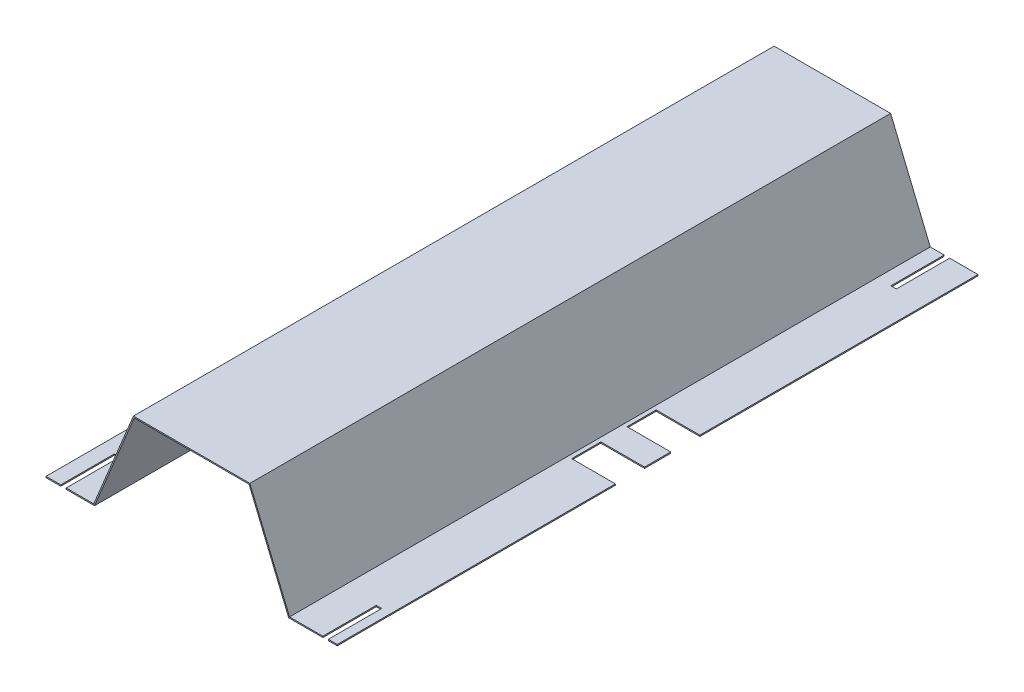
SolidWorks part; units mm, degrees
material "6061-T6 (SS)"
ref_plane "Front" through (0, 0, 0) normal (0, 0, 1) x (1, 0, 0)
ref_plane "Top" through (0, 0, 0) normal (0, 1, 0) x (1, 0, 0)
ref_plane "Right" through (0, 0, 0) normal (1, 0, 0) x (0, 0, -1)
sketch "Sketch1" plane through (0, 0, 0) normal (0, 0, 1) x (1, 0, 0)
  line L0 (-0.2237, 63.6222) -> (51.6461, 189.022)
  line L1 (51.6461, 189.022) -> (204.0461, 189.022)
  line L2 (254.8461, 62.022) -> (318.3461, 62.022)
  line L3 (204.0461, 189.022) -> (255.9159, 63.6222)
  line L4 (254.8461, 62.022) -> (202.9763, 187.4218)
  line L5 (0.8461, 62.022) -> (-62.6539, 62.022)
  line L6 (202.9763, 187.4218) -> (52.7159, 187.4218)
  line L7 (52.7159, 187.4218) -> (0.8461, 62.022)
  line L8 (318.3461, 62.022) -> (318.3461, 63.6222)
  line L9 (318.3461, 63.6222) -> (255.9159, 63.6222)
  line L10 (-62.6539, 62.022) -> (-62.6539, 63.6222)
  line L11 (-62.6539, 63.6222) -> (-0.2237, 63.6222)
  dimension "D1" = 1.6002
  dimension "D2" = 1.6002
  dimension "D3" = 254
  dimension "D4" = 152.4
  dimension "D5" = 1.6002
  dimension "D6" = 1.6002
  dimension "D7" = 63.5
  dimension "D8" = 63.5
  dimension "D9" = 127
extrude "Boss-Extrude1" add sketch "Sketch1" along normal blind 838.2
sketch "Sketch4" plane through (0, 63.6222, 0) normal (0, 1, 0) x (1, 0, 0)
  line L0 (318.3461, -838.2) -> (318.3461, 0) construction
  line L1 (318.3461, -363.855) -> (261.1961, -363.855)
  line L2 (318.3461, -363.855) -> (318.3461, -401.955)
  line L3 (318.3461, -401.955) -> (261.1961, -401.955)
  line L4 (261.1961, -363.855) -> (261.1961, -401.955)
  line L5 (318.3461, -419.1) -> (-62.6539, -419.1) construction
  line L6 (318.3461, -474.345) -> (261.1961, -474.345)
  line L7 (318.3461, -474.345) -> (318.3461, -436.245)
  line L8 (318.3461, -436.245) -> (261.1961, -436.245)
  line L9 (261.1961, -474.345) -> (261.1961, -436.245)
  line L10 (-62.6539, -838.2) -> (-62.6539, 0) construction
  line L11 (289.7711, -401.955) -> (289.7711, -419.1) construction
  line L12 (289.7711, -436.245) -> (289.7711, -419.1) construction
  dimension "D1" = 57.15
  dimension "D2" = 57.15
  dimension "D3" = 38.1
  dimension "D4" = 38.1
  dimension "D5" = 34.29
extrude "Cut-Extrude3" cut sketch "Sketch4" against normal blind 2.54
sketch "Sketch5" plane through (0, 63.6222, 0) normal (0, 1, 0) x (1, 0, 0)
  line L0 (-0.2237, 0) -> (-62.6539, 0) construction
  line L1 (-30.6499, 0) -> (-23.5379, 0)
  line L2 (-30.6499, 0) -> (-30.6499, -69.85)
  line L3 (-30.6499, -69.85) -> (-23.5379, -69.85)
  line L4 (-23.5379, 0) -> (-23.5379, -69.85)
  line L5 (-62.6539, -838.2) -> (-62.6539, 0) construction
  line L6 (-0.2237, -838.2) -> (-62.6539, -838.2) construction
  line L7 (-43.3499, -838.2) -> (-36.2379, -838.2)
  line L8 (-43.3499, -838.2) -> (-43.3499, -768.35)
  line L9 (-43.3499, -768.35) -> (-36.2379, -768.35)
  line L10 (-36.2379, -838.2) -> (-36.2379, -768.35)
  line L11 (318.3461, -838.2) -> (255.9159, -838.2) construction
  line L13 (318.3461, 0) -> (255.9159, 0) construction
  line L14 (274.1501, 0) -> (281.2621, 0)
  line L16 (274.1501, 0) -> (274.1501, -69.85)
  line L17 (274.1501, -69.85) -> (281.2621, -69.85)
  line L18 (281.2621, 0) -> (281.2621, -69.85)
  line L20 (299.5501, -838.2) -> (306.6621, -838.2)
  line L21 (299.5501, -838.2) -> (299.5501, -768.35)
  line L22 (299.5501, -768.35) -> (306.6621, -768.35)
  line L23 (306.6621, -838.2) -> (306.6621, -768.35)
  dimension "D10" = 7.112
  dimension "D11" = 19.304
  dimension "D8" = 69.85
  dimension "D9" = 7.112
  dimension "D1" = 7.112
  dimension "D2" = 69.85
  dimension "D3" = 32.004
  dimension "D4" = 69.85
  dimension "D5" = 7.112
  dimension "D6" = 297.688
  dimension "D7" = 69.85
  dimension "D12" = 335.788
extrude "Cut-Extrude4" cut sketch "Sketch5" against normal through all
